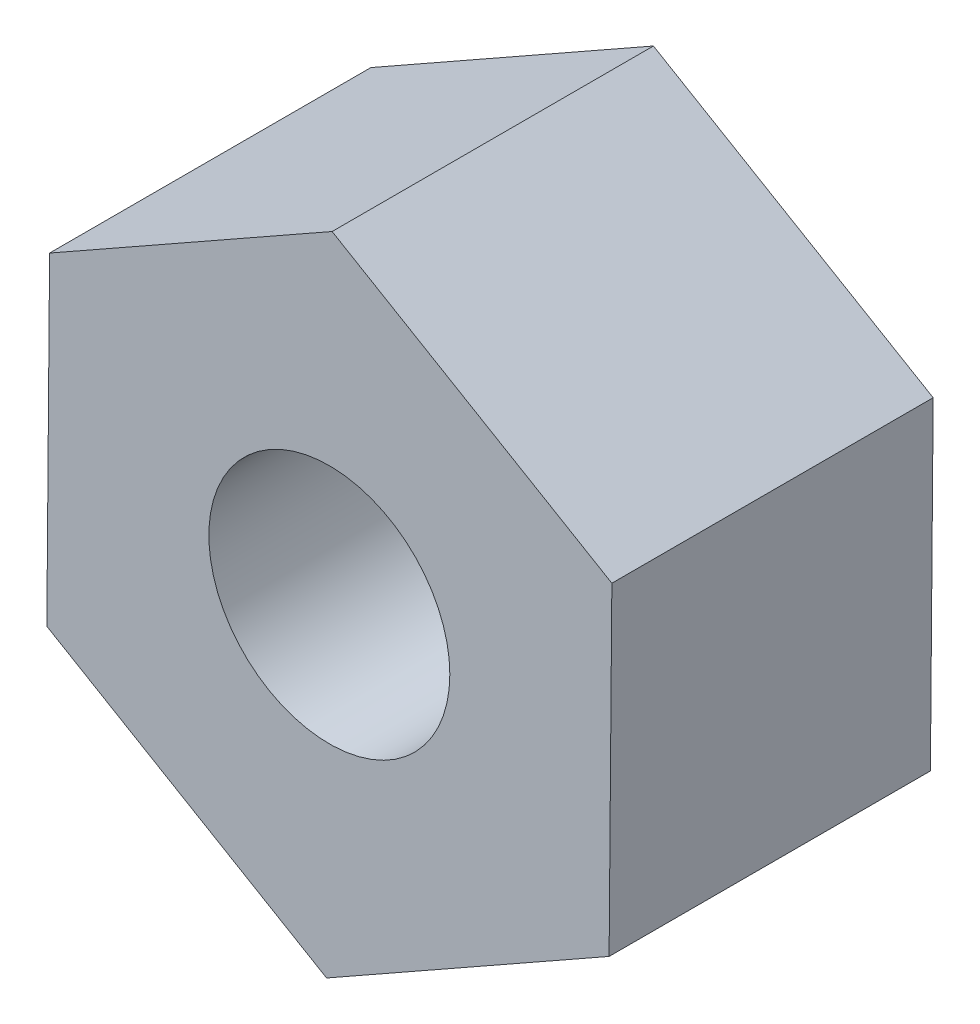
SolidWorks part; units mm, degrees
ref_plane "Front Plane" through (0, 0, 0) normal (0, 0, 1) x (1, 0, 0)
ref_plane "Top Plane" through (0, 0, 0) normal (0, 1, 0) x (1, 0, 0)
ref_plane "Right Plane" through (0, 0, 0) normal (1, 0, 0) x (0, 0, -1)
sketch "Sketch1" plane through (0, 0, 0) normal (0, 0, 1) x (1, 0, 0)
  line L1 (-3.4827, 2.0505) -> (-3.5171, -1.9908)
  line L2 (-3.5171, -1.9908) -> (-0.0344, -4.0413)
  line L3 (-0.0344, -4.0413) -> (3.4827, -2.0505)
  line L4 (3.4827, -2.0505) -> (3.5171, 1.9908)
  line L5 (3.5171, 1.9908) -> (0.0344, 4.0413)
  line L6 (0.0344, 4.0413) -> (-3.4827, 2.0505)
  circle A0 centre (0, 0) radius 3.5 construction
  circle A1 centre (0, 0) radius 1.5
  dimension "D1" = 7
  dimension "D2" = 3
extrude "Boss-Extrude2" add sketch "Sketch1" along normal blind 4
